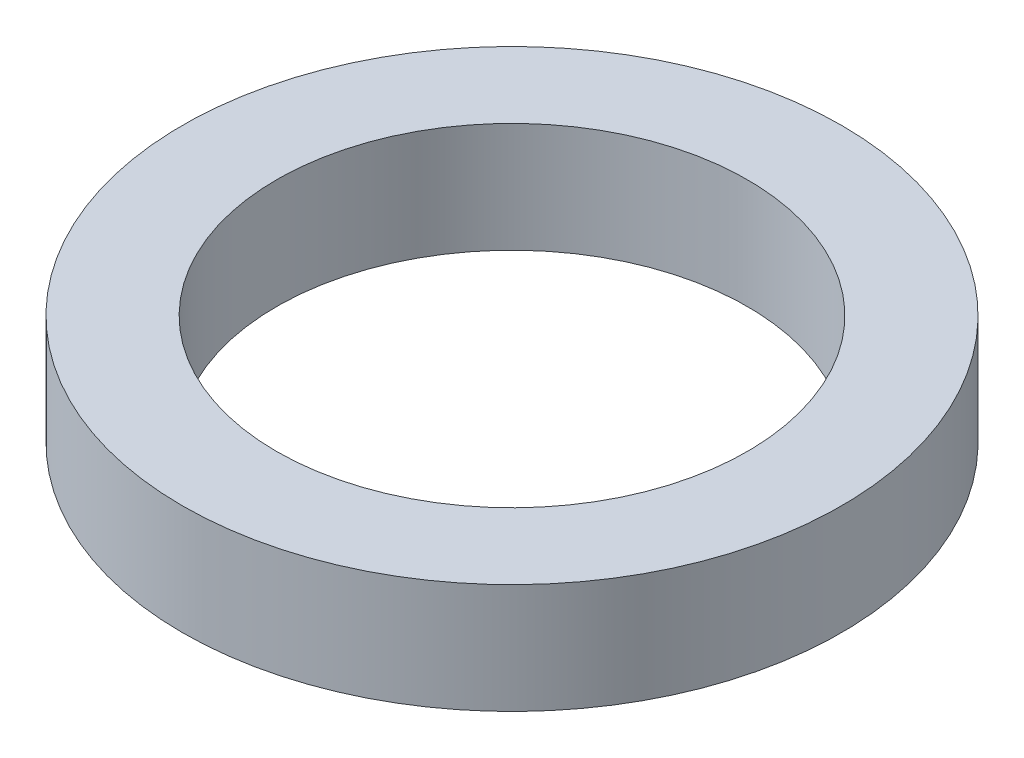
SolidWorks part; units mm, degrees
ref_plane "Front Plane" through (0, 0, 0) normal (0, 0, 1) x (1, 0, 0)
ref_plane "Top Plane" through (0, 0, 0) normal (0, 1, 0) x (1, 0, 0)
ref_plane "Right Plane" through (0, 0, 0) normal (1, 0, 0) x (0, 0, -1)
sketch "Sketch1" plane through (0, 0, 0) normal (0, 0, 1) x (1, 0, 0)
  line L0 (0, 0) -> (18, 0) construction
  line L1 (0, 3.5) -> (0, -3.5) construction
  line L2 (21, -3.5) -> (15, -3.5)
  line L3 (21, -3.5) -> (21, 3.5)
  line L4 (21, 3.5) -> (15, 3.5)
  line L5 (15, -3.5) -> (15, 3.5)
  line L6 (21, -3.5) -> (15, 3.5) construction
  line L7 (21, 3.5) -> (15, -3.5) construction
  point P9 (0, -7.0659)
  point P10 (0, 0)
  dimension "D1" = 7
  dimension "D2" = 15
  dimension "D3" = 21
revolve "Revolve1" add sketch "Sketch1" angle 360 about L1
